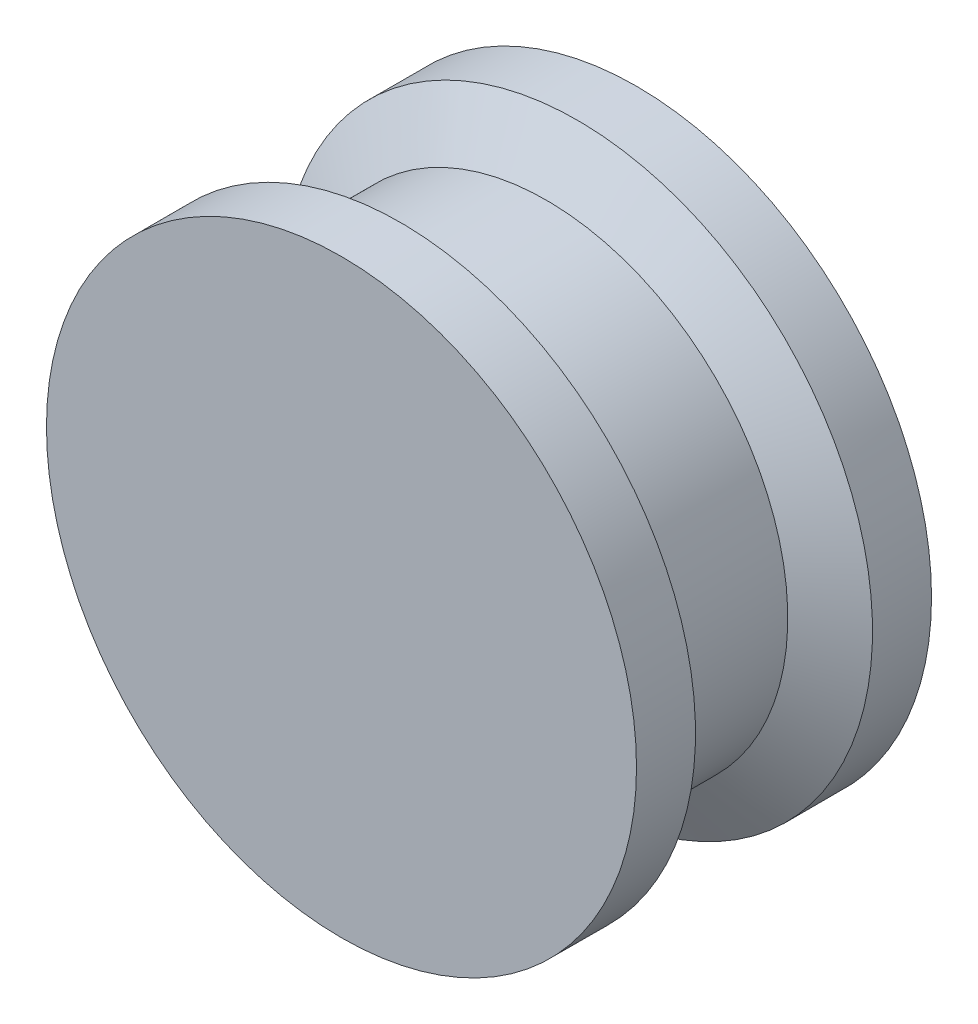
SolidWorks part; units mm, degrees
ref_plane "Front Plane" through (0, 0, 0) normal (0, 0, 1) x (1, 0, 0)
ref_plane "Top Plane" through (0, 0, 0) normal (0, 1, 0) x (1, 0, 0)
ref_plane "Right Plane" through (0, 0, 0) normal (1, 0, 0) x (0, 0, -1)
sketch "Sketch1" plane through (0, 0, 0) normal (0, 0, 1) x (1, 0, 0)
  circle A0 centre (0, 0) radius 10
  dimension "D1" = 20
extrude "Boss-Extrude1" add sketch "Sketch1" along normal mid plane 10
sketch "Sketch2" plane through (0, 0, 0) normal (0, 1, 0) x (1, 0, 0)
  line L0 (0, 0) -> (11.9548, 0) construction
  line L1 (10, 3) -> (8.1786, 1.9484)
  line L2 (10, -5) -> (10, 5) construction
  line L3 (8.1786, 1.9484) -> (8.1786, -1.9484)
  line L4 (10, -3) -> (8.1786, -1.9484)
  line L5 (10, 3) -> (10, -3)
  line L6 (0, 6.3879) -> (0, -5.8087) construction
  point P9 (8.1786, 0)
  dimension "D1" = 120
  dimension "D2" = 2
revolve "Cut-Revolve1" cut sketch "Sketch2" angle 360 about L6
